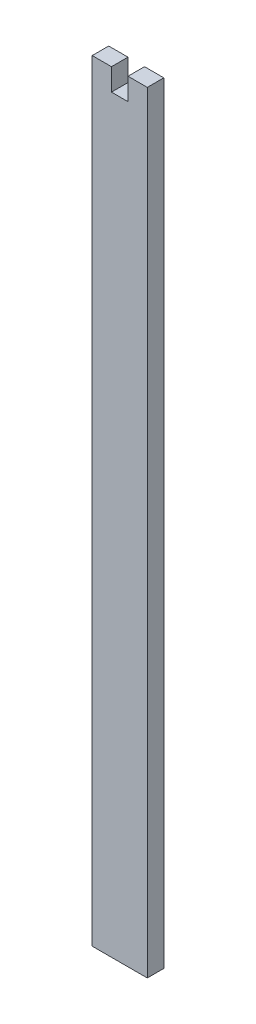
SolidWorks part; units mm, degrees
ref_plane "Front Plane" through (0, 0, 0) normal (0, 0, 1) x (1, 0, 0)
ref_plane "Top Plane" through (0, 0, 0) normal (0, 1, 0) x (1, 0, 0)
ref_plane "Right Plane" through (0, 0, 0) normal (1, 0, 0) x (0, 0, -1)
sketch "Sketch1" plane through (0, 0, 0) normal (0, 0, 1) x (1, 0, 0)
  line L0 (1.5, 70) -> (5, 70)
  line L1 (-5, 70) -> (-1.5, 70)
  line L2 (-5, 70) -> (-5, -70)
  line L3 (-5, -70) -> (5, -70)
  line L4 (5, 70) -> (5, -70)
  line L5 (-5, 70) -> (5, -70) construction
  line L6 (-5, -70) -> (5, 70) construction
  line L7 (-1.5, 70) -> (-1.5, 66)
  line L8 (-1.5, 66) -> (1.5, 66)
  line L9 (1.5, 66) -> (1.5, 70)
  point P0 (0, 0)
  dimension "D1" = 140
  dimension "D2" = 10
  dimension "D3" = 4
  dimension "D4" = 3.5
  dimension "D5" = 3.5
extrude "Boss-Extrude1" add sketch "Sketch1" along normal mid plane 3
